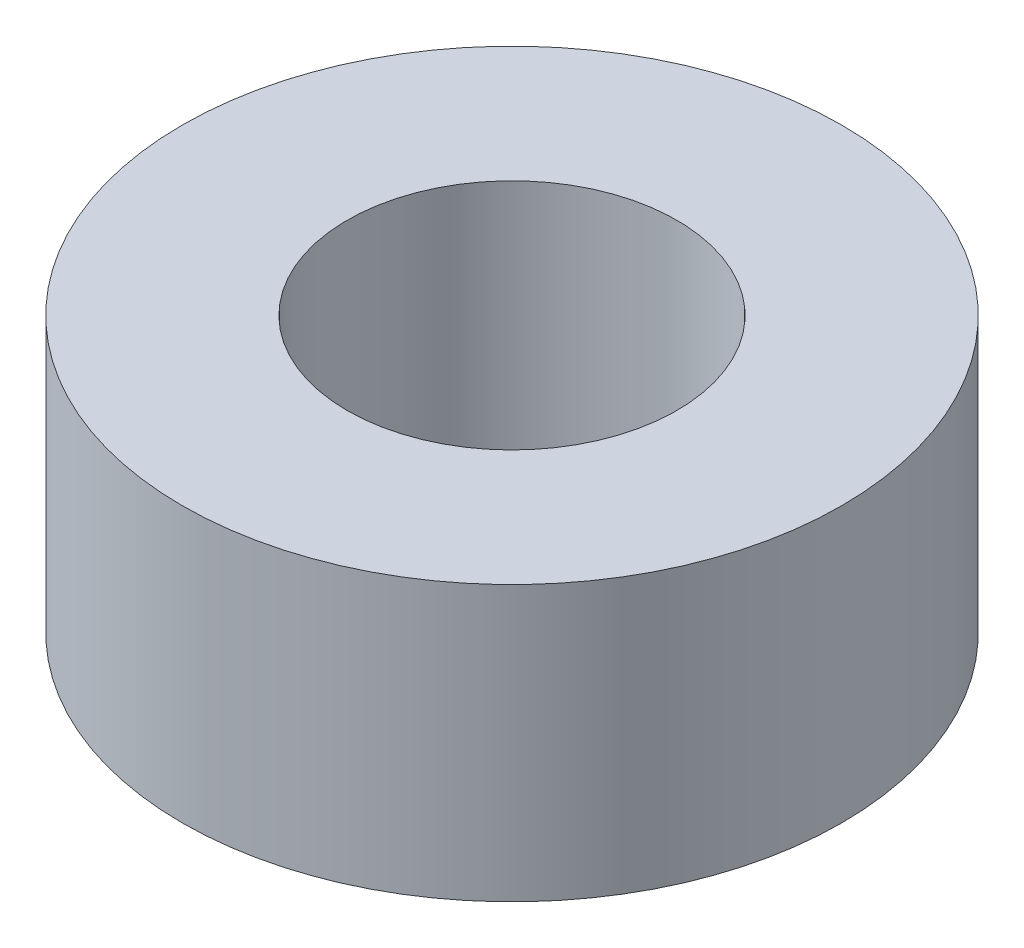
SolidWorks part; units mm, degrees
ref_plane "Front Plane" through (0, 0, 0) normal (0, 0, 1) x (1, 0, 0)
ref_plane "Top Plane" through (0, 0, 0) normal (0, 1, 0) x (1, 0, 0)
ref_plane "Right Plane" through (0, 0, 0) normal (1, 0, 0) x (0, 0, -1)
other "Bounding Box"
ref_plane "Default Plane" through (13.8565, 3.175, 6.7999) normal (0, -1, 0) x (-1, 0, 0)
sketch "Sketch1" plane through (0, 0, 0) normal (0, 1, 0) x (1, 0, 0)
  circle A0 centre (0, 0) radius 1.5
  circle A1 centre (0, 0) radius 3
  dimension "D1" = 6
  dimension "D2" = 3
extrude "Boss-Extrude1" add sketch "Sketch1" along normal blind 2.5
